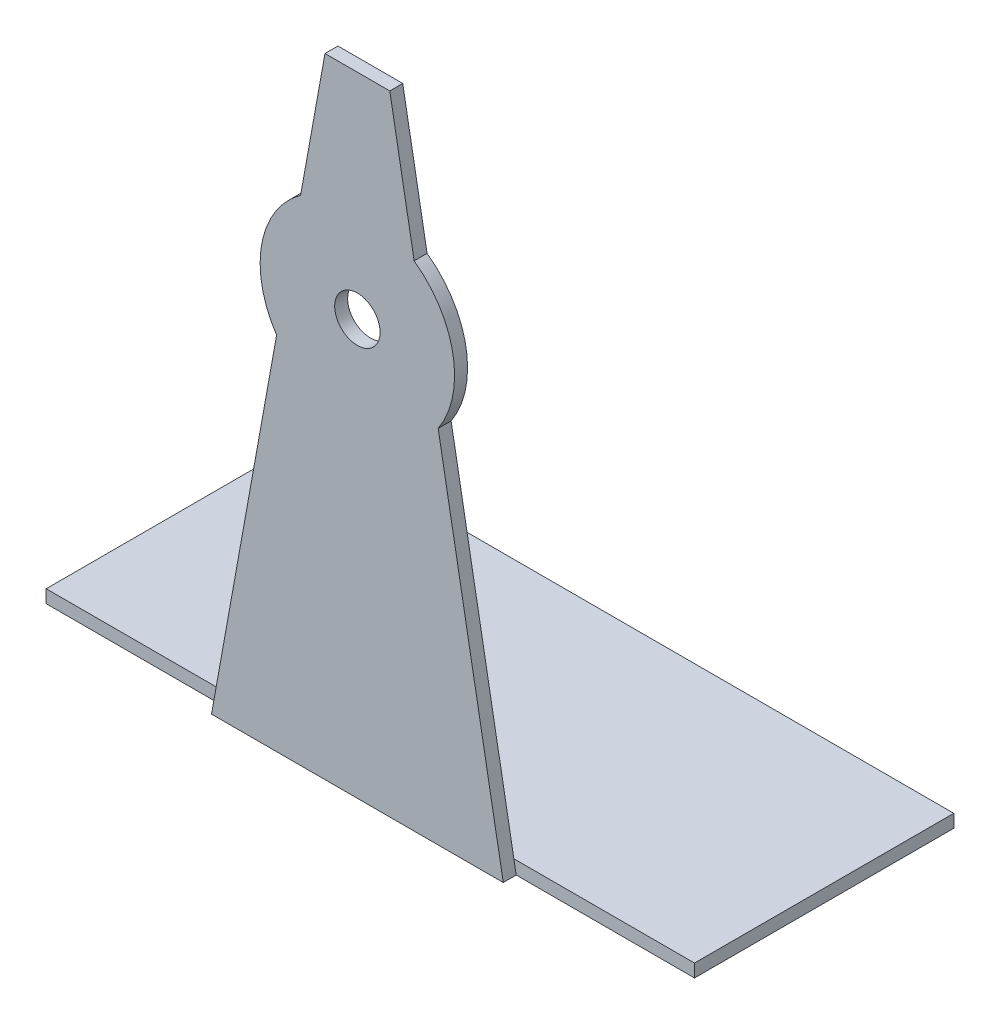
SolidWorks part; units mm, degrees
ref_plane "前视基准面" through (0, 0, 0) normal (0, 0, 1) x (1, 0, 0)
ref_plane "上视基准面" through (0, 0, 0) normal (0, 1, 0) x (1, 0, 0)
ref_plane "右视基准面" through (0, 0, 0) normal (1, 0, 0) x (0, 0, -1)
sketch "草图1" plane through (0, 0, 0) normal (0, 1, 0) x (1, 0, 0)
  line L1 (0, 0) -> (100, 0)
  line L2 (0, 0) -> (0, 40)
  line L3 (0, 40) -> (100, 40)
  line L4 (100, 0) -> (100, 40)
  dimension "D1" = 100
  dimension "D2" = 40
extrude "凸台-拉伸1" add sketch "草图1" along normal blind 2
sketch "草图3" plane through (0, 0, 0) normal (0, 0, 1) x (1, 0, 0)
  line L0 (50, 2) -> (50, 127.0667) construction
  line L1 (0, 2) -> (100, 2) construction
  line L2 (72.5, 0) -> (27.5, 0)
  line L3 (27.5, 0) -> (37.5397, 55.6488)
  line L4 (41.2436, 76.1789) -> (45, 97)
  line L5 (45, 97) -> (55, 97)
  line L6 (58.7564, 76.1789) -> (55, 97)
  line L7 (72.5, 0) -> (62.4603, 55.6488)
  line L8 (0, 0) -> (100, 0) construction
  arc A0 (41.2436, 76.1789) -> (37.5397, 55.6488) centre (50, 64) ccw
  arc A1 (58.7564, 76.1789) -> (62.4603, 55.6488) centre (50, 64) cw
  point P13 (50, 97)
  dimension "D3" = 15
  dimension "D1" = 45
  dimension "D2" = 62
  dimension "D4" = 95
  dimension "D5" = 10
extrude "凸台-拉伸2" add sketch "草图3" along normal blind 2
sketch "草图4" plane through (0, 0, 2) normal (0, 0, 1) x (1, 0, 0)
  circle A0 centre (50, 64) radius 3.5
  dimension "D1" = 7
extrude "切除-拉伸1" cut sketch "草图4" against normal blind 2
